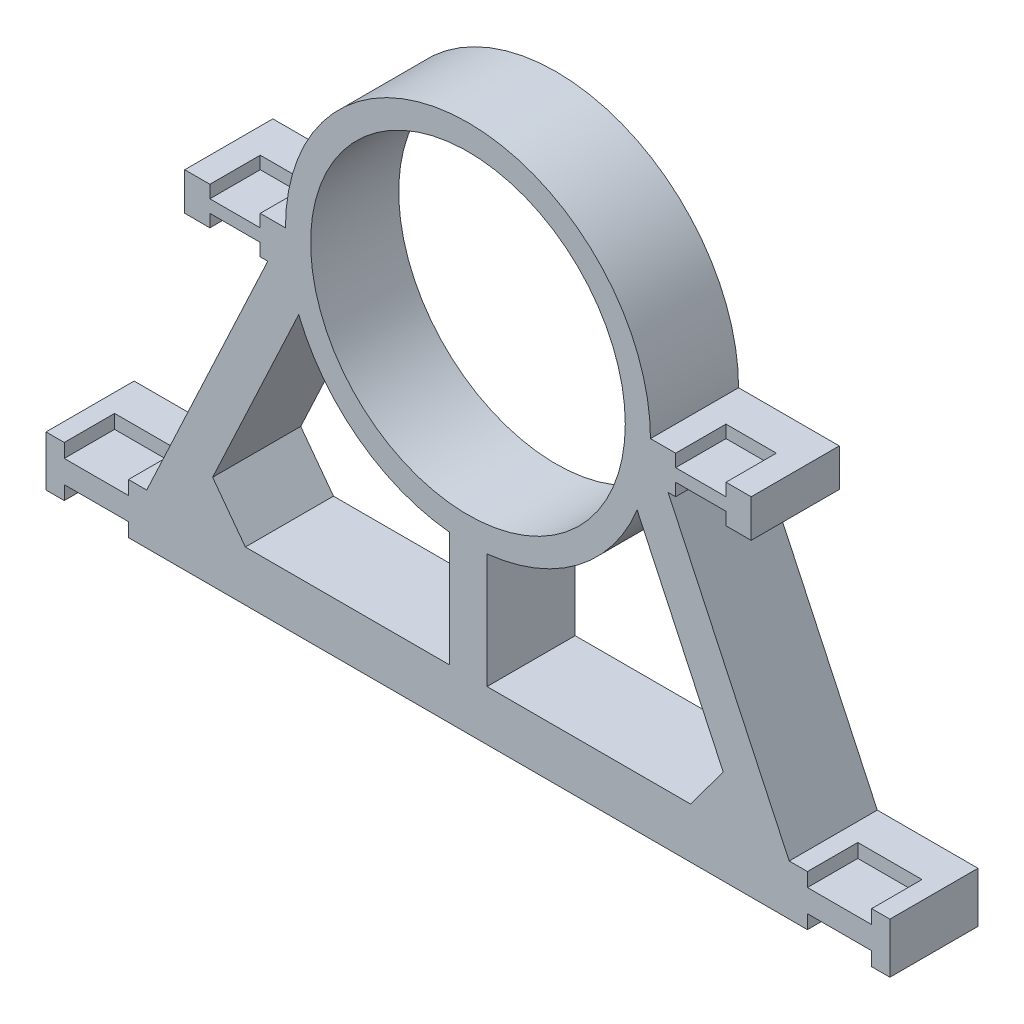
SolidWorks part; units mm, degrees
material "1023 Carbon Steel Sheet (SS)"
ref_plane "Ön Düzlem" through (0, 0, 0) normal (0, 0, 1) x (1, 0, 0)
ref_plane "Üst Düzlem" through (0, 0, 0) normal (0, 1, 0) x (1, 0, 0)
ref_plane "Sağ Düzlem" through (0, 0, 0) normal (1, 0, 0) x (0, 0, -1)
sketch "Sketch1" plane through (0, 0, 0) normal (0, 0, 1) x (1, 0, 0)
  line L0 (-72.5, 0) -> (-127.6009, -117.745)
  line L1 (-127.6009, -117.745) -> (-109.6009, -117.745)
  line L2 (-109.6009, -117.745) -> (-67.2156, -27.1719)
  line L3 (-109.6009, -117.745) -> (109.6009, -117.745)
  line L4 (0, -117.745) -> (0, -137.745)
  line L5 (167.6009, -137.745) -> (-167.6009, -137.745)
  line L6 (-167.6009, -137.745) -> (-167.6009, -117.745)
  line L7 (-167.6009, -117.745) -> (-127.6009, -117.745)
  line L8 (-7.4061, -72.1207) -> (-7.4061, -117.745)
  line L10 (7.5939, -72.1012) -> (7.5939, -117.745)
  line L11 (-101.4175, -100.2578) -> (-88.4083, -117.745)
  line L12 (-101.4175, -100.2578) -> (-119.4175, -100.2578)
  line L13 (101.4175, -100.2578) -> (119.4175, -100.2578)
  line L14 (101.4175, -100.2578) -> (88.4083, -117.745)
  line L15 (109.6009, -117.745) -> (67.2156, -27.1719)
  line L16 (72.5, 0) -> (127.6009, -117.745)
  line L17 (167.6009, -137.745) -> (167.6009, -117.745)
  line L18 (167.6009, -117.745) -> (127.6009, -117.745)
  line L19 (127.6009, -117.745) -> (109.6009, -117.745)
  line L20 (7.4061, -72.1207) -> (7.4061, -117.745)
  circle A0 centre (0, 0) radius 62.5
  circle A1 centre (0, 0) radius 72.5
  dimension "D1" = 125
  dimension "D2" = 10
  dimension "D3" = 100
  dimension "D4" = 130
  dimension "D5" = 18
  dimension "D6" = 40
  dimension "D7" = 167.6009
  dimension "D8" = 15
  dimension "D9" = 20
  dimension "D10" = 45.6243
  dimension "D11" = 21.7955
  dimension "D12" = 17.4872
extrude "Boss-Extrude8" add sketch "Sketch1" along normal blind 35 contours A1 A0 | A1 L0 L12 L2 | L2 L12 L0 L1 | L11 L2 L3 | L7 L6 L5 L4 L3 L1 | L18 L19 L3 L4 L5 L17 | L3 L15 L14 | L19 L16 L13 L15 | A1 L15 L13 L16
sketch "Sketch2" plane through (0, -117.745, 0) normal (0, 1, 0) x (1, 0, 0)
  line L0 (-7.4061, 0) -> (-7.4061, -35)
  line L1 (-88.4083, -35) -> (88.4083, -35) construction
  line L2 (-7.4061, 0) -> (7.5939, 0)
  line L3 (7.5939, 0) -> (7.5939, -35)
  line L4 (7.5939, -35) -> (-7.4061, -35)
extrude "Boss-Extrude9" add sketch "Sketch2" along normal up to surface (45.6243 mm away)
ref_plane "Plane3" through (72.5, 0, 0) normal (1, 0, 0) x (0, 0, -1)
sketch "Sketch6" plane through (72.5, 0, 0) normal (1, 0, 0) x (0, 0, -1)
  line L0 (19.25, 0) -> (-19.25, 0) construction
  line L1 (-35, 0) -> (0, 0)
  line L2 (-35, 0) -> (-35, -15)
  line L3 (-35, -15) -> (0, -15)
  line L4 (0, 0) -> (0, -15)
  line L5 (-35, 72.5) -> (-35, 0) construction
  line L6 (0, 72.5) -> (0, -72.5) construction
  dimension "D1" = 35
  dimension "D2" = 15
ref_plane "Plane5" through (-72.5, 0, 0) normal (1, 0, 0) x (0, 0, -1)
sketch "Sketch10" plane through (-72.5, 0, 0) normal (1, 0, 0) x (0, 0, -1)
  line L0 (-35, 0) -> (-35, -117.745) construction
  line L1 (0, 0) -> (-35, 0)
  line L2 (0, 0) -> (0, -15)
  line L3 (0, -15) -> (-35, -15)
  line L4 (-35, 0) -> (-35, -15)
  dimension "D1" = 35
  dimension "D2" = 15
extrude "Boss-Extrude12" add sketch "Sketch10" against normal blind 40
extrude "Boss-Extrude10" add sketch "Sketch6" along normal blind 40
sketch "Sketch11" plane through (0, 0, 35) normal (0, 0, 1) x (1, 0, 0)
  line L0 (-112.5, 0) -> (-72.5, 0) construction
  line L1 (-102.5, 0) -> (-82.5, 0)
  line L2 (-102.5, 0) -> (-102.5, -5)
  line L3 (-102.5, -5) -> (-82.5, -5)
  line L4 (-82.5, 0) -> (-82.5, -5)
  line L5 (-112.5, -15) -> (-79.5195, -15) construction
  line L6 (-102.5, -15) -> (-82.5, -15)
  line L7 (-102.5, -15) -> (-102.5, -10)
  line L8 (-102.5, -10) -> (-82.5, -10)
  line L9 (-82.5, -15) -> (-82.5, -10)
  line L10 (112.5, 0) -> (72.5, 0) construction
  line L11 (82.5, 0) -> (102.5, 0)
  line L12 (82.5, 0) -> (82.5, -5)
  line L13 (82.5, -5) -> (102.5, -5)
  line L14 (102.5, 0) -> (102.5, -5)
  line L15 (112.5, -15) -> (79.5195, -15) construction
  line L16 (82.5, -15) -> (102.5, -15)
  line L17 (82.5, -15) -> (82.5, -10)
  line L18 (82.5, -10) -> (102.5, -10)
  line L19 (102.5, -15) -> (102.5, -10)
  line L20 (167.6009, -117.745) -> (127.6009, -117.745) construction
  line L21 (134.8509, -117.745) -> (160.3509, -117.745)
  line L22 (134.8509, -117.745) -> (134.8509, -123.245)
  line L23 (134.8509, -123.245) -> (160.3509, -123.245)
  line L24 (160.3509, -117.745) -> (160.3509, -123.245)
  line L25 (167.6009, -137.745) -> (-167.6009, -137.745) construction
  line L26 (160.3509, -137.745) -> (134.8509, -137.745)
  line L27 (160.3509, -137.745) -> (160.3509, -132.245)
  line L28 (160.3509, -132.245) -> (134.8509, -132.245)
  line L29 (134.8509, -137.745) -> (134.8509, -132.245)
  line L30 (-167.6009, -117.745) -> (-127.6009, -117.745) construction
  line L31 (-160.3509, -117.745) -> (-134.8509, -117.745)
  line L32 (-160.3509, -117.745) -> (-160.3509, -123.245)
  line L33 (-160.3509, -123.245) -> (-134.8509, -123.245)
  line L34 (-134.8509, -117.745) -> (-134.8509, -123.245)
  line L35 (112.5, 0) -> (112.5, -15) construction
  line L36 (-160.3509, -137.745) -> (-134.8509, -137.745)
  line L37 (-160.3509, -137.745) -> (-160.3509, -132.245)
  line L38 (-160.3509, -132.245) -> (-134.8509, -132.245)
  line L39 (-134.8509, -137.745) -> (-134.8509, -132.245)
  dimension "D1" = 20
  dimension "D2" = 10
  dimension "D3" = 5
  dimension "D4" = 5
  dimension "D5" = 10
  dimension "D6" = 20
  dimension "D7" = 25.5
  dimension "D8" = 7.25
  dimension "D9" = 5.5
  dimension "D10" = 5.5
  dimension "D11" = 25.5
  dimension "D12" = 7.25
  dimension "D13" = 20
  dimension "D14" = 10
  dimension "D15" = 10
  dimension "D16" = 20
  dimension "D17" = 5
  dimension "D18" = 5
  dimension "D19" = 7.25
  dimension "D20" = 7.25
  dimension "D21" = 25.5
  dimension "D22" = 25.5
  dimension "D23" = 5.5
  dimension "D24" = 5.5
extrude "Cut-Extrude1" cut sketch "Sketch11" against normal blind 20
